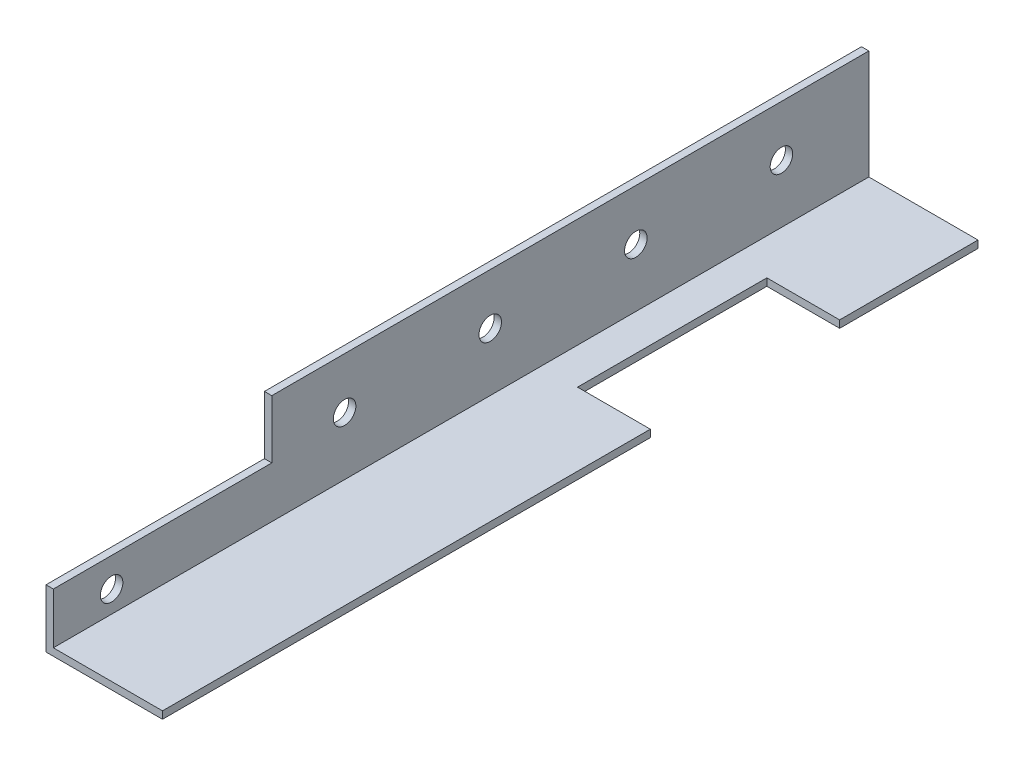
SolidWorks part; units mm, degrees
ref_plane "Front Plane" through (0, 0, 0) normal (0, 0, 1) x (1, 0, 0)
ref_plane "Top Plane" through (0, 0, 0) normal (0, 1, 0) x (1, 0, 0)
ref_plane "Right Plane" through (0, 0, 0) normal (1, 0, 0) x (0, 0, -1)
sketch "Sketch1" plane through (0, 0, 0) normal (0, 0, 1) x (1, 0, 0)
  line L0 (0, 0) -> (0, 25.4)
  line L1 (0, 25.4) -> (1.6002, 25.4)
  line L2 (1.6002, 25.4) -> (1.6002, 1.6002)
  line L3 (1.6002, 1.6002) -> (25.4, 1.6002)
  line L4 (25.4, 1.6002) -> (25.4, 0)
  line L5 (25.4, 0) -> (0, 0)
  dimension "D1" = 1.6002
  dimension "D2" = 25.4
extrude "Boss-Extrude1" add sketch "Sketch1" along normal blind 177.8 contours L2 L3 L4 L5 L0 L1
hole_wizard "#10 (0.1935) Diameter Hole1" positions "Sketch3" profile "Sketch2" hole size "#10" standard "ANSI Inch" end condition through all
sketch "Sketch3" plane through (1.6002, 0, 0) normal (1, 0, 0) x (0, 0, -1)
  line L1 (0, 25.4) -> (0, 1.6002) construction
  line L5 (-177.8, 0) -> (0, 0) construction
  point P0 (-82.55, 14.2875)
  point P2 (-50.8, 14.2875)
  point P4 (-19.05, 14.2875)
  point P9 (0, 13.5001)
  point P16 (0, 13.5001)
  point P27 (-114.3, 14.2875)
  dimension "D1" = 82.55
  dimension "D2" = 19.05
  dimension "D3" = 50.8
  dimension "D4" = 14.2875
  dimension "D5" = 31.75
sketch "Sketch2" plane through (1.6002, 14.2875, 82.55) normal (0, 1, 0) x (0, 0, -1)
  line L0 (0, 0) -> (0, 1.6002)
  line L1 (0, 1.6002) -> (2.4574, 1.6002)
  line L2 (2.4574, 1.6002) -> (2.4574, 0)
  line L5 (2.4574, 0) -> (0, 0)
  line L11 (0, -6.35) -> (0, 107.95) construction
  dimension "Thru Hole Dia." = 4.9149
  dimension "Thru Hole Depth" = 1.6002
sketch "Sketch4" plane through (0, 1.6002, 0) normal (0, 1, 0) x (1, 0, 0)
  line L0 (1.6002, 0) -> (25.4, 0) construction
  line L1 (25.4, -177.8) -> (25.4, 0) construction
  line L4 (9.525, -30.1625) -> (25.4, -30.1625)
  line L5 (9.525, -30.1625) -> (9.525, -71.4375)
  line L6 (9.525, -71.4375) -> (25.4, -71.4375)
  line L7 (25.4, -30.1625) -> (25.4, -71.4375)
  line L8 (9.525, -30.1625) -> (25.4, -71.4375) construction
  line L9 (9.525, -71.4375) -> (25.4, -30.1625) construction
  point P6 (17.4625, -50.8)
  dimension "D1" = 15.875
  dimension "D2" = 41.275
  dimension "D3" = 50.8
extrude "Cut-Extrude1" cut sketch "Sketch4" against normal through all
sketch "Sketch5" plane through (1.6002, 0, 0) normal (1, 0, 0) x (0, 0, -1)
  line L1 (-177.8, 25.4) -> (-130.175, 25.4)
  line L2 (-177.8, 25.4) -> (-177.8, 12.7)
  line L3 (-177.8, 12.7) -> (-130.175, 12.7)
  line L4 (-130.175, 25.4) -> (-130.175, 12.7)
  dimension "D1" = 47.625
  dimension "D2" = 12.7
extrude "Cut-Extrude2" cut sketch "Sketch5" against normal through all
hole_wizard "#10 (0.1935) Diameter Hole2" positions "Sketch7" profile "Sketch6" hole size "#10" standard "ANSI Inch" end condition through all
sketch "Sketch7" plane through (1.6002, 0, 0) normal (1, 0, 0) x (0, 0, -1)
  line L0 (-177.8, 12.7) -> (-177.8, 1.6002) construction
  line L1 (-177.8, 12.7) -> (-130.175, 12.7) construction
  point P0 (-165.1, 6.35)
  dimension "D1" = 12.7
  dimension "D2" = 6.35
sketch "Sketch6" plane through (1.6002, 6.35, 165.1) normal (0, 1, 0) x (0, 0, -1)
  line L0 (0, 0) -> (0, 1.6002)
  line L1 (0, 1.6002) -> (2.4574, 1.6002)
  line L2 (2.4574, 1.6002) -> (2.4574, 0)
  line L5 (2.4574, 0) -> (0, 0)
  line L11 (0, -6.35) -> (0, 107.95) construction
  dimension "Thru Hole Dia." = 4.9149
  dimension "Thru Hole Depth" = 1.6002
